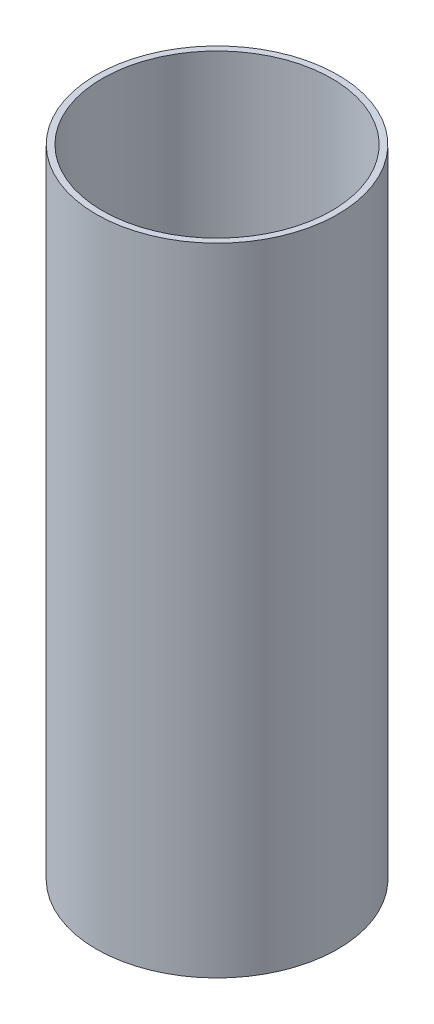
SolidWorks part; units mm, degrees
material "PVC Rigid"
ref_plane "Front Plane" through (0, 0, 0) normal (0, 0, 1) x (1, 0, 0)
ref_plane "Top Plane" through (0, 0, 0) normal (0, 1, 0) x (1, 0, 0)
ref_plane "Right Plane" through (0, 0, 0) normal (1, 0, 0) x (0, 0, -1)
sketch "Sketch1" plane through (0, 0, 0) normal (0, 1, 0) x (1, 0, 0)
  circle A0 centre (0, 0) radius 93.6625
  circle A1 centre (0, 0) radius 88.9
  dimension "D1" = 187.325
  dimension "D2" = 177.8
extrude "Boss-Extrude1" add sketch "Sketch1" along normal mid plane 493.428
